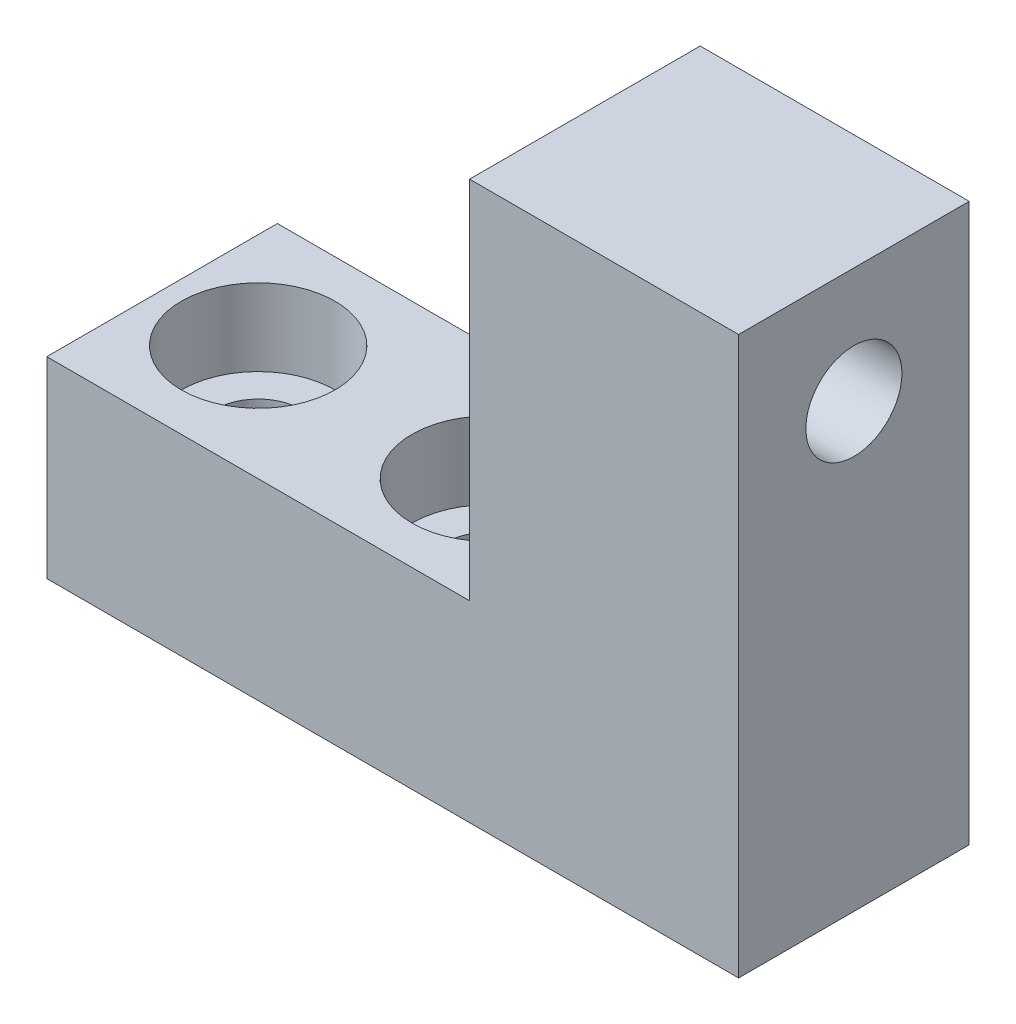
SolidWorks part; units mm, degrees
ref_plane "Front Plane" through (0, 0, 0) normal (0, 0, 1) x (1, 0, 0)
ref_plane "Top Plane" through (0, 0, 0) normal (0, 1, 0) x (1, 0, 0)
ref_plane "Right Plane" through (0, 0, 0) normal (1, 0, 0) x (0, 0, -1)
sketch "Sketch1" plane through (0, 0, 0) normal (0, 0, 1) x (1, 0, 0)
  line L1 (-8.2774, 3.0437) -> (27.7226, 3.0437)
  line L2 (-8.2774, 3.0437) -> (-8.2774, -6.9563)
  line L3 (-8.2774, -6.9563) -> (27.7226, -6.9563)
  line L4 (27.7226, 3.0437) -> (27.7226, -6.9563)
  dimension "D1" = 36
  dimension "D2" = 10
extrude "Boss-Extrude1" add sketch "Sketch1" along normal blind 12
sketch "Sketch2" plane through (0, 3.0437, 0) normal (0, 1, 0) x (1, 0, 0)
  line L0 (27.7226, 0) -> (-8.2774, 0) construction
  line L1 (27.7226, -12) -> (13.7226, -12)
  line L2 (27.7226, -12) -> (27.7226, 0)
  line L3 (27.7226, 0) -> (13.7226, 0)
  line L4 (13.7226, -12) -> (13.7226, 0)
  dimension "D1" = 14
extrude "Boss-Extrude2" add sketch "Sketch2" along normal blind 19
sketch "Sketch3" plane through (0, 3.0437, 0) normal (0, 1, 0) x (1, 0, 0)
  line L0 (-8.2774, -12) -> (-8.2774, 0) construction
  line L1 (27.7226, -12) -> (27.7226, 0) construction
  circle A0 centre (-3.2774, -6) radius 2.25
  circle A1 centre (8.7226, -6) radius 2.25
  point P6 (-8.2774, -6)
  dimension "D1" = 4.5
  dimension "D2" = 5
  dimension "D3" = 19
extrude "Cut-Extrude1" cut sketch "Sketch3" against normal through all
sketch "Sketch4" plane through (0, 3.0437, 0) normal (0, 1, 0) x (1, 0, 0)
  circle A0 centre (-3.2774, -6) radius 4
  circle A1 centre (8.7226, -6) radius 4
  dimension "D1" = 8
  dimension "D2" = 8
extrude "Cut-Extrude2" cut sketch "Sketch4" against normal blind 4
hole_wizard "M6 Tapped Hole1" positions "Sketch5" profile "Sketch6" tap size "M6" standard "ISO" end condition through all
sketch "Sketch5" plane through (27.7226, 0, 0) normal (1, 0, 0) x (0, 0, -1)
  line L0 (-12, 22.0437) -> (0, 22.0437) construction
  point P0 (-6, 16.0437)
  dimension "D1" = 6
cosmetic thread "Hole Thread1" parameters "D2"=6
sketch "Sketch6" plane through (27.7226, 16.0437, 6) normal (0, 1, 0) x (0, 0, -1)
  line L0 (0, 0) -> (0, 36)
  line L1 (0, 36) -> (2.5, 36)
  line L2 (2.5, 36) -> (2.5, 0)
  line L5 (2.5, 0) -> (0, 0)
  line L11 (0, -6.35) -> (0, 107.95) construction
  dimension "Thru Tap Drill Dia." = 5
  dimension "Thru Tap Drill Depth" = 36
